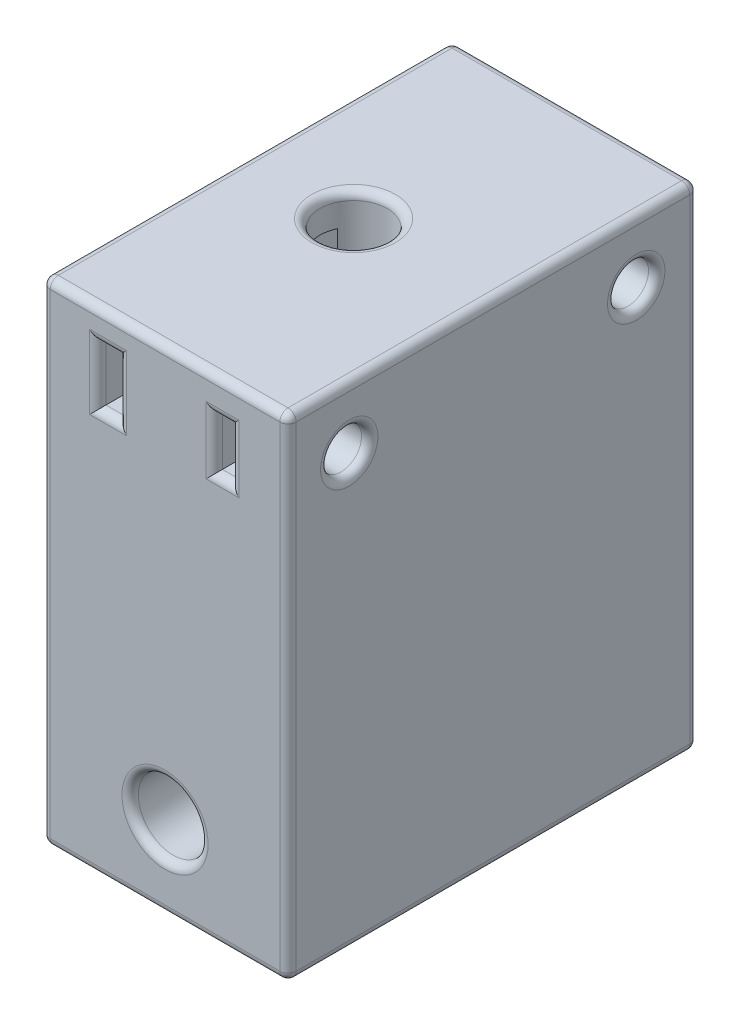
SolidWorks part; units mm, degrees
ref_plane "前视基准面" through (0, 0, 0) normal (0, 0, 1) x (1, 0, 0)
ref_plane "上视基准面" through (0, 0, 0) normal (0, 1, 0) x (1, 0, 0)
ref_plane "右视基准面" through (0, 0, 0) normal (1, 0, 0) x (0, 0, -1)
sketch "草图1" plane through (0, 0, 0) normal (0, 0, 1) x (1, 0, 0)
  line L1 (-8.6305, 51.447) -> (21.3695, 51.447)
  line L2 (-8.6305, 51.447) -> (-8.6305, -8.553)
  line L3 (-8.6305, -8.553) -> (21.3695, -8.553)
  line L4 (21.3695, 51.447) -> (21.3695, -8.553)
  circle A0 centre (6.3695, 1.447) radius 4.25
  dimension "D3" = 8.5
  dimension "D1" = 30
  dimension "D2" = 60
  dimension "D4" = 10
extrude "凸台-拉伸1" add sketch "草图1" along normal blind 50
sketch "草图2" plane through (0, 0, 50) normal (0, 0, 1) x (1, 0, 0)
  line L0 (21.3695, -8.553) -> (21.3695, 51.447) construction
  line L1 (-1.8305, 47.647) -> (0.6695, 47.647)
  line L2 (-1.8305, 47.647) -> (-1.8305, 40.647)
  line L3 (-1.8305, 40.647) -> (0.6695, 40.647)
  line L4 (0.6695, 47.647) -> (0.6695, 40.647)
  line L5 (12.3695, 47.147) -> (14.3695, 47.147)
  line L6 (12.3695, 47.147) -> (12.3695, 40.947)
  line L7 (12.3695, 40.947) -> (14.3695, 40.947)
  line L8 (14.3695, 47.147) -> (14.3695, 40.947)
  line L9 (-8.6305, 51.447) -> (-8.6305, -8.553) construction
  line L10 (21.3695, 51.447) -> (-8.6305, 51.447) construction
  dimension "D1" = 7
  dimension "D2" = 6.8
  dimension "D3" = 2.5
  dimension "D4" = 2
  dimension "D5" = 6.2
  dimension "D6" = 7
  dimension "D7" = 4.3
  dimension "D8" = 3.8
extrude "切除-拉伸1" cut sketch "草图2" against normal blind 50
sketch "草图4" plane through (21.3695, 0, 0) normal (1, 0, 0) x (0, 0, -1)
  line L0 (-50, 51.447) -> (0, 51.447) construction
  circle A0 centre (-42.5325, 43.947) radius 2.5
  circle A1 centre (-7.5325, 43.947) radius 2.5
  dimension "D1" = 5
  dimension "D2" = 7.5
  dimension "D3" = 2
extrude "切除-拉伸2" cut sketch "草图4" against normal blind 7 and the other way through all
fillet "圆角1" radius 1 4 edges at (13.3695, 40.947, 50) (12.3695, 44.047, 50) (13.3695, 47.147, 50) (14.3695, 44.047, 50)
fillet "圆角2" radius 1 4 edges at (-0.5805, 40.647, 50) (-1.8305, 44.147, 50) (-0.5805, 47.647, 50) (0.6695, 44.147, 50)
fillet "圆角3" radius 1 1 edges at (10.6195, 1.447, 50)
fillet "圆角4" radius 1 1 edges at (21.3695, 41.447, 42.5325)
fillet "圆角5" radius 1 1 edges at (21.3695, 41.447, 7.5325)
fillet "圆角6" radius 1 9 edges at (-0.5805, 40.647, 0) (0.6695, 44.147, 0) (-1.8305, 44.147, 0) (-0.5805, 47.647, 0) (13.3695, 40.947, 0) (14.3695, 44.047, 0) (13.3695, 47.147, 0) (12.3695, 44.047, 0) (10.6195, 1.447, 0)
sketch "草图5" plane through (0, 51.447, 0) normal (0, 1, 0) x (1, 0, 0)
  line L0 (21.3695, -50) -> (21.3695, 0) construction
  line L1 (-8.6305, -50) -> (-8.6305, 0) construction
  line L2 (21.3695, -50) -> (-8.6305, -50) construction
  circle A0 centre (4.3695, -25) radius 4.1
  dimension "D1" = 8.2
  dimension "D2" = 13
extrude "切除-拉伸3" cut sketch "草图5" against normal blind 36
fillet "圆角7" radius 1 1 edges at (4.3695, 51.447, 29.1)
fillet "圆角8" radius 1 12 edges at (-8.6305, -8.553, 25) (6.3695, -8.553, 0) (-8.6305, 21.447, 0) (21.3695, 21.447, 0) (21.3695, -8.553, 25) (6.3695, -8.553, 50) (-8.6305, 21.447, 50) (21.3695, 21.447, 50) (6.3695, 51.447, 0) (-8.6305, 51.447, 25) (6.3695, 51.447, 50) (21.3695, 51.447, 25)
